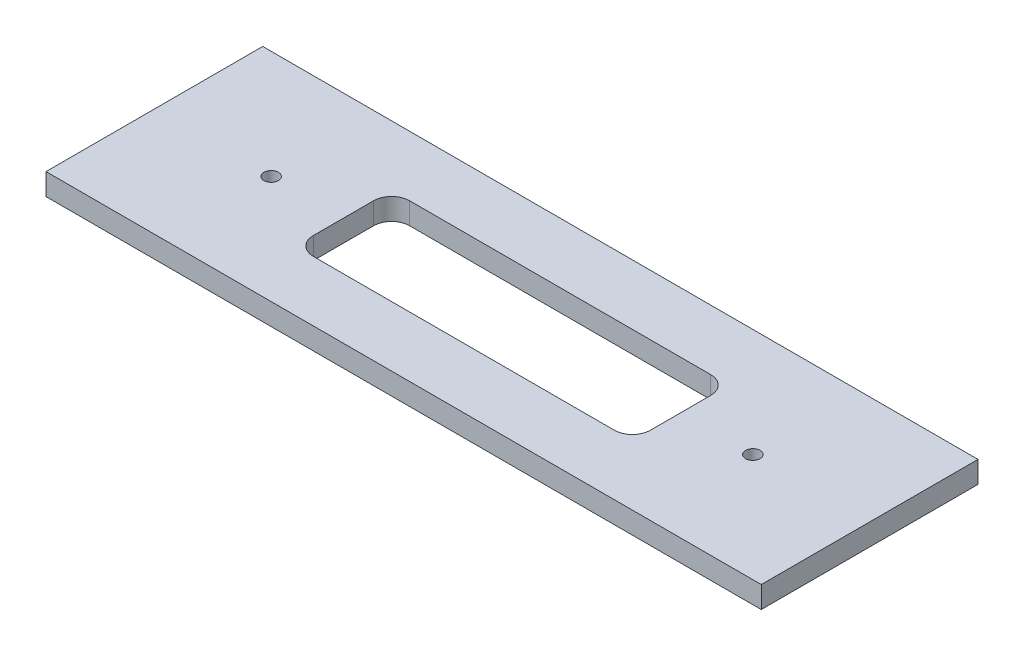
SolidWorks part; units mm, degrees
ref_plane "Front Plane" through (0, 0, 0) normal (0, 0, 1) x (1, 0, 0)
ref_plane "Top Plane" through (0, 0, 0) normal (0, 1, 0) x (1, 0, 0)
ref_plane "Right Plane" through (0, 0, 0) normal (1, 0, 0) x (0, 0, -1)
sketch "Sketch1" plane through (0, 0, 0) normal (0, 1, 0) x (1, 0, 0)
  line L1 (-297, -90) -> (297, -90)
  line L2 (-297, -90) -> (-297, 90)
  line L3 (-297, 90) -> (297, 90)
  line L4 (297, -90) -> (297, 90)
  line L5 (-297, -90) -> (297, 90) construction
  line L6 (-297, 90) -> (297, -90) construction
  point P0 (0, 0)
  dimension "D1" = 594
  dimension "D2" = 180
extrude "Boss-Extrude1" add sketch "Sketch1" along normal blind 18
sketch "Sketch2" plane through (0, 18, 0) normal (0, 1, 0) x (1, 0, 0)
  line L1 (-125, -40) -> (125, -40)
  line L2 (-140, -25) -> (-140, 25)
  line L3 (-125, 40) -> (125, 40)
  line L4 (140, -25) -> (140, 25)
  line L5 (-140, -40) -> (140, 40) construction
  line L6 (-140, 40) -> (140, -40) construction
  arc A0 (-125, -40) -> (-140, -25) centre (-125, -25) cw
  arc A1 (125, -40) -> (140, -25) centre (125, -25) ccw
  arc A2 (125, 40) -> (140, 25) centre (125, 25) cw
  arc A3 (-140, 25) -> (-125, 40) centre (-125, 25) cw
  circle A4 centre (-200, 0) radius 6
  circle A5 centre (200, 0) radius 6
  point P0 (0, 0)
  dimension "D3" = 15
  dimension "D4" = 12
  dimension "D5" = 12
  dimension "D6" = 200
  dimension "D7" = 200
  dimension "D1" = 80
  dimension "D2" = 280
extrude "Cut-Extrude1" cut sketch "Sketch2" against normal blind 40
